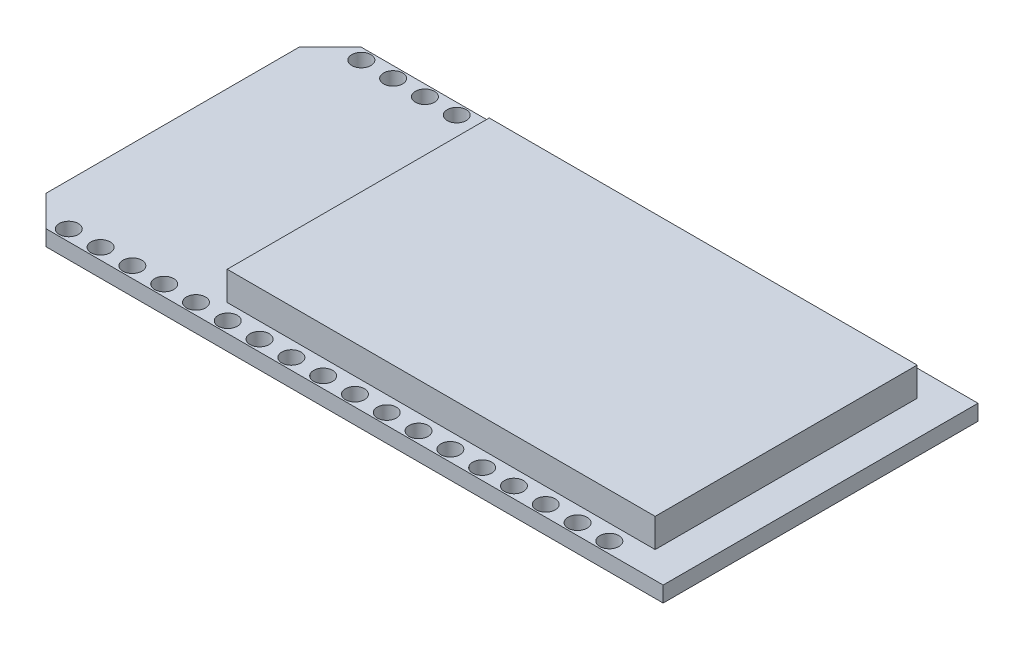
SolidWorks part; units mm, degrees
ref_plane "Plan de face" through (0, 0, 0) normal (0, 0, 1) x (1, 0, 0)
ref_plane "Plan de dessus" through (0, 0, 0) normal (0, 1, 0) x (1, 0, 0)
ref_plane "Plan de droite" through (0, 0, 0) normal (1, 0, 0) x (0, 0, -1)
sketch "Esquisse1" plane through (0, 0, 0) normal (0, 1, 0) x (1, 0, 0)
  line L1 (0, 0) -> (51.75, 0)
  line L2 (0, 0) -> (0, 25.15)
  line L3 (0, 25.15) -> (51.75, 25.15)
  line L4 (51.75, 0) -> (51.75, 25.15)
  dimension "D1" = 51.75
  dimension "D2" = 25.15
extrude "Boss.-Extru.1" add sketch "Esquisse1" along normal blind 1.25
sketch "Esquisse2" plane through (0, 1.25, 0) normal (0, 1, 0) x (1, 0, 0)
  line L0 (0, 25.15) -> (2.45, 25.15)
  line L1 (51.75, 25.15) -> (0, 25.15) construction
  line L2 (0, 25.15) -> (0, 22.7)
  line L3 (0, 25.15) -> (0, 0) construction
  line L4 (0, 22.7) -> (2.45, 25.15)
  line L5 (0, 0) -> (2.45, 0)
  line L6 (0, 0) -> (51.75, 0) construction
  line L7 (0, 0) -> (0, 2.45)
  line L8 (0, 2.45) -> (2.45, 0)
  dimension "D1" = 2.45
  dimension "D2" = 2.45
  dimension "D3" = 2.45
extrude "Enlèv. mat.-Extru.1" cut sketch "Esquisse2" against normal blind 1.25
sketch "Esquisse3" plane through (0, 1.25, 0) normal (0, 1, 0) x (1, 0, 0)
  line L0 (0, 22.7) -> (3.38, 22.7) construction
  line L1 (3.38, 25.15) -> (3.38, 24.26) construction
  line L2 (51.75, 25.15) -> (2.45, 25.15) construction
  line L3 (0, 12.575) -> (51.75, 12.575) construction
  line L4 (0, 22.7) -> (0, 2.45) construction
  line L5 (51.75, 0) -> (51.75, 25.15) construction
  circle A0 centre (3.38, 24.26) radius 0.762
  circle A1 centre (5.92, 24.26) radius 0.762
  circle A2 centre (8.46, 24.26) radius 0.762
  circle A3 centre (11, 24.26) radius 0.762
  circle A4 centre (13.54, 24.26) radius 0.762
  circle A5 centre (16.08, 24.26) radius 0.762
  circle A6 centre (18.62, 24.26) radius 0.762
  circle A7 centre (21.16, 24.26) radius 0.762
  circle A8 centre (23.7, 24.26) radius 0.762
  circle A9 centre (26.24, 24.26) radius 0.762
  circle A10 centre (28.78, 24.26) radius 0.762
  circle A11 centre (31.32, 24.26) radius 0.762
  circle A12 centre (33.86, 24.26) radius 0.762
  circle A13 centre (36.4, 24.26) radius 0.762
  circle A14 centre (38.94, 24.26) radius 0.762
  circle A15 centre (41.48, 24.26) radius 0.762
  circle A16 centre (44.02, 24.26) radius 0.762
  circle A17 centre (46.56, 24.26) radius 0.762
  circle A18 centre (46.56, 0.89) radius 0.762
  circle A19 centre (44.02, 0.89) radius 0.762
  circle A20 centre (41.48, 0.89) radius 0.762
  circle A21 centre (38.94, 0.89) radius 0.762
  circle A22 centre (36.4, 0.89) radius 0.762
  circle A23 centre (33.86, 0.89) radius 0.762
  circle A24 centre (31.32, 0.89) radius 0.762
  circle A25 centre (28.78, 0.89) radius 0.762
  circle A26 centre (26.24, 0.89) radius 0.762
  circle A27 centre (23.7, 0.89) radius 0.762
  circle A28 centre (18.62, 0.89) radius 0.762
  circle A29 centre (21.16, 0.89) radius 0.762
  circle A30 centre (16.08, 0.89) radius 0.762
  circle A31 centre (13.54, 0.89) radius 0.762
  circle A32 centre (11, 0.89) radius 0.762
  circle A33 centre (8.46, 0.89) radius 0.762
  circle A34 centre (5.92, 0.89) radius 0.762
  circle A35 centre (3.38, 0.89) radius 0.762
  dimension "D3" = 18
  dimension "D1" = 3.38
  dimension "D2" = 0.89
extrude "Enlèv. mat.-Extru.2" cut sketch "Esquisse3" against normal blind 1.25
sketch "Esquisse4" plane through (0, 1.25, 0) normal (0, 1, 0) x (1, 0, 0)
  line L1 (14.7924, 23.0647) -> (48.9791, 23.0647)
  line L2 (14.7924, 23.0647) -> (14.7924, 2.1312)
  line L3 (14.7924, 2.1312) -> (48.9791, 2.1312)
  line L4 (48.9791, 23.0647) -> (48.9791, 2.1312)
extrude "Boss.-Extru.2" add sketch "Esquisse4" along normal blind 2.3
